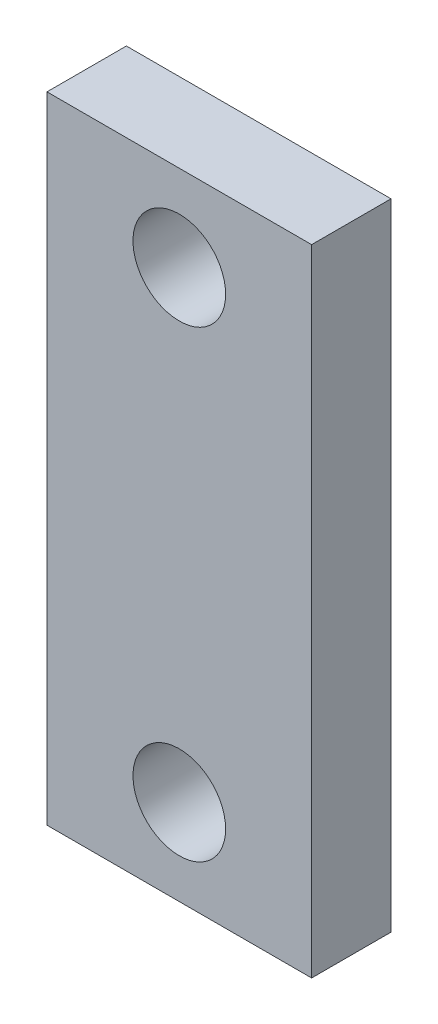
SolidWorks part; units mm, degrees
ref_plane "Alzado" through (0, 0, 0) normal (0, 0, 1) x (1, 0, 0)
ref_plane "Planta" through (0, 0, 0) normal (0, 1, 0) x (1, 0, 0)
ref_plane "Vista lateral" through (0, 0, 0) normal (1, 0, 0) x (0, 0, -1)
sketch "Croquis1" plane through (0, 0, 0) normal (0, 0, 1) x (1, 0, 0)
  line L1 (-5, -12) -> (5, -12)
  line L2 (-5, -12) -> (-5, 12)
  line L3 (-5, 12) -> (5, 12)
  line L4 (5, -12) -> (5, 12)
  line L5 (-5, -12) -> (5, 12) construction
  line L6 (-5, 12) -> (5, -12) construction
  circle A0 centre (0, 8.75) radius 1.75
  circle A1 centre (0, -8.75) radius 1.75
  point P0 (0, 0)
  dimension "D1" = 3.5
  dimension "D2" = 3.5
  dimension "D3" = 8.75
  dimension "D4" = 8.75
  dimension "D5" = 24
  dimension "D6" = 10
extrude "Saliente-Extruir1" add sketch "Croquis1" along normal blind 3
